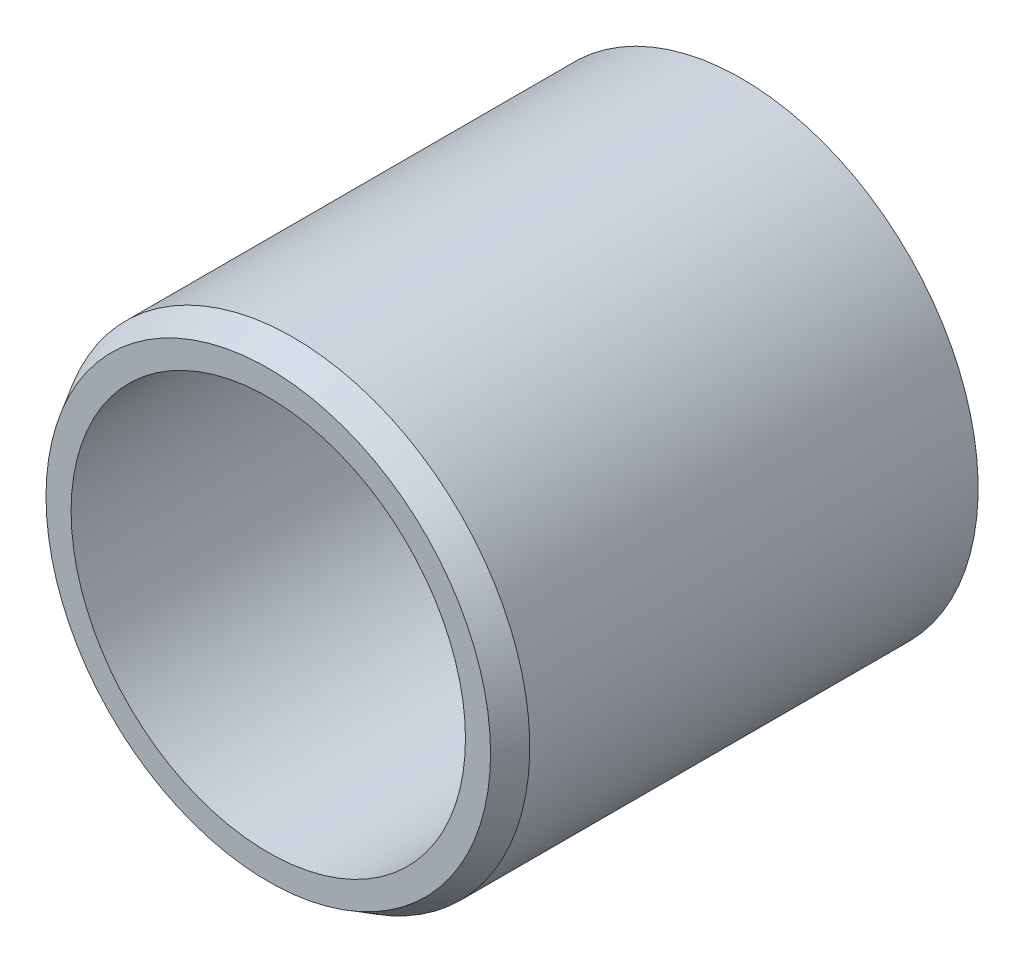
SolidWorks part; units mm, degrees
ref_plane "Front Plane" through (0, 0, 0) normal (0, 0, 1) x (1, 0, 0)
ref_plane "Top Plane" through (0, 0, 0) normal (0, 1, 0) x (1, 0, 0)
ref_plane "Right Plane" through (0, 0, 0) normal (1, 0, 0) x (0, 0, -1)
ref_plane "Plane1" through (0, 0, 0) normal (0, -1, 0) x (1, 0, 0)
sketch "Sketch1" plane through (0, 0, 0) normal (0, -1, 0) x (1, 0, 0)
  line L0 (4.4738, 9.525) -> (3.9688, 9.525)
  line L1 (3.9688, 9.525) -> (3.9688, 0.5)
  line L2 (3.9688, 0.5) -> (4.2574, 0)
  line L3 (4.2574, 0) -> (4.7625, 0)
  line L4 (4.7625, 0) -> (4.7625, 9.025)
  line L5 (4.7625, 9.025) -> (4.4738, 9.525)
  line L6 (0, 9.525) -> (0, 0) construction
revolve "Revolve1" add sketch "Sketch1" angle 360 about L6
